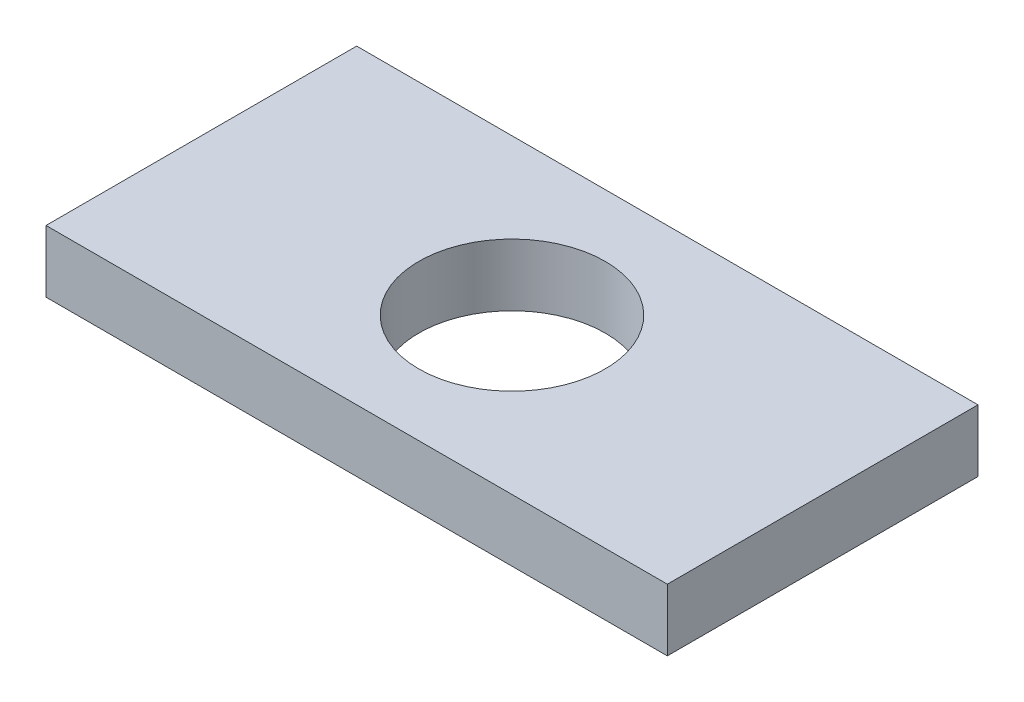
SolidWorks part; units mm, degrees
ref_plane "Спереди" through (0, 0, 0) normal (0, 0, 1) x (1, 0, 0)
ref_plane "Сверху" through (0, 0, 0) normal (0, 1, 0) x (1, 0, 0)
ref_plane "Справа" through (0, 0, 0) normal (1, 0, 0) x (0, 0, -1)
sketch "Эскиз1" plane through (0, 0, 0) normal (0, 1, 0) x (1, 0, 0)
  line L1 (0, 0) -> (40, 0)
  line L2 (0, 0) -> (0, 20)
  line L3 (0, 20) -> (40, 20)
  line L4 (40, 0) -> (40, 20)
extrude "Бобышка-Вытянуть1" add sketch "Эскиз1" along normal blind 4
sketch "Эскиз2" plane through (0, 4, 0) normal (0, 1, 0) x (1, 0, 0)
  circle A0 centre (20, 10) radius 6
extrude "Вырез-Вытянуть1" cut sketch "Эскиз2" against normal through all
